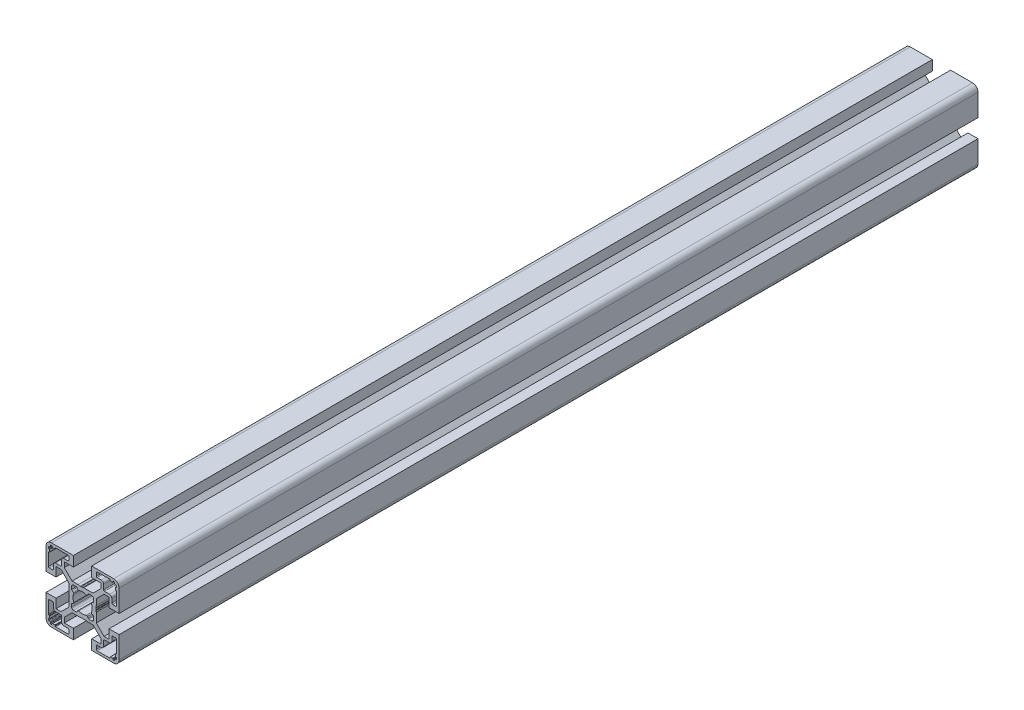
SolidWorks part; units mm, degrees
ref_plane "Front Plane" through (0, 0, 0) normal (0, 0, 1) x (1, 0, 0)
ref_plane "Top Plane" through (0, 0, 0) normal (0, 1, 0) x (1, 0, 0)
ref_plane "Right Plane" through (0, 0, 0) normal (1, 0, 0) x (0, 0, -1)
sketch "Sketch1" plane through (0, 0, 0) normal (0, 0, 1) x (1, 0, 0)
  line L0 (-11.7678, -10) -> (-14.5, -10)
  line L1 (-14.5, -10) -> (-14.5, -5)
  line L2 (-14.5, -5) -> (-20, -5)
  line L3 (-20, -5) -> (-20, -17)
  line L4 (-17, -20) -> (-5, -20)
  line L5 (-5, -20) -> (-5, -14.5)
  line L6 (-5, -14.5) -> (-10, -14.5)
  line L7 (-10, -14.5) -> (-10, -11.7678)
  line L8 (-10, -11.7678) -> (-5.7322, -7.5)
  line L9 (-5.7322, -7.5) -> (-0.6536, -7.5)
  line L10 (-0.4036, -7.433) -> (0, -7.2)
  line L11 (0, -7.2) -> (0.4036, -7.433)
  line L12 (0.9036, -7.433) -> (1.2189, -7.251)
  line L13 (1.2189, -7.251) -> (2.5, -7.5)
  line L14 (2.5, -7.5) -> (5.7322, -7.5)
  line L15 (5.7322, -7.5) -> (10, -11.7678)
  line L16 (10, -11.7678) -> (10, -14.5)
  line L17 (10, -14.5) -> (5, -14.5)
  line L18 (5, -14.5) -> (5, -20)
  line L19 (5, -20) -> (17, -20)
  line L20 (20, -17) -> (20, -5)
  line L21 (20, -5) -> (14.5, -5)
  line L22 (14.5, -5) -> (14.5, -10)
  line L23 (14.5, -10) -> (11.7678, -10)
  line L24 (11.7678, -10) -> (7.5, -5.7322)
  line L25 (7.5, -5.7322) -> (7.5, -0.6536)
  line L26 (7.433, -0.4036) -> (7.2, 0)
  line L27 (7.2, 0) -> (7.433, 0.4036)
  line L28 (7.433, 0.9036) -> (7.251, 1.2189)
  line L29 (7.251, 1.2189) -> (7.5, 2.5)
  line L30 (7.5, 2.5) -> (7.5, 5.7322)
  line L31 (7.5, 5.7322) -> (11.7678, 10)
  line L32 (11.7678, 10) -> (14.5, 10)
  line L33 (14.5, 10) -> (14.5, 5)
  line L34 (14.5, 5) -> (20, 5)
  line L35 (20, 5) -> (20, 17)
  line L36 (17, 20) -> (5, 20)
  line L37 (5, 20) -> (5, 14.5)
  line L38 (5, 14.5) -> (10, 14.5)
  line L39 (10, 14.5) -> (10, 11.7678)
  line L40 (10, 11.7678) -> (5.7322, 7.5)
  line L41 (5.7322, 7.5) -> (0.6536, 7.5)
  line L42 (0.4036, 7.433) -> (0, 7.2)
  line L43 (0, 7.2) -> (-0.4036, 7.433)
  line L44 (-0.9036, 7.433) -> (-1.2189, 7.251)
  line L45 (-1.2189, 7.251) -> (-2.5, 7.5)
  line L46 (-2.5, 7.5) -> (-5.7322, 7.5)
  line L47 (-5.7322, 7.5) -> (-10, 11.7678)
  line L48 (-10, 11.7678) -> (-10, 14.5)
  line L49 (-10, 14.5) -> (-5, 14.5)
  line L50 (-5, 14.5) -> (-5, 20)
  line L51 (-5, 20) -> (-17, 20)
  line L52 (-20, 17) -> (-20, 5)
  line L53 (-20, 5) -> (-14.5, 5)
  line L54 (-14.5, 5) -> (-14.5, 10)
  line L55 (-14.5, 10) -> (-11.7678, 10)
  line L56 (-11.7678, 10) -> (-7.5, 5.7322)
  line L57 (-7.5, 5.7322) -> (-7.5, 0.6536)
  line L58 (-7.433, 0.4036) -> (-7.2, 0)
  line L59 (-7.2, 0) -> (-7.433, -0.4036)
  line L60 (-7.433, -0.9036) -> (-7.251, -1.2189)
  line L61 (-7.251, -1.2189) -> (-7.5, -2.5)
  line L62 (-7.5, -2.5) -> (-7.5, -5.7322)
  line L63 (-7.5, -5.7322) -> (-11.7678, -10)
  line L64 (7.5, 16.5) -> (7.5, 18.2)
  line L65 (8, 18.7) -> (14.8, 18.7)
  line L66 (15, 18.5) -> (15, 18.2)
  line L67 (15.2, 18) -> (16.4, 18)
  line L68 (16.6, 18.2) -> (16.6, 18.5)
  line L69 (16.8, 18.7) -> (17.3, 18.7)
  line L70 (17.6, 18.4) -> (17.6, 17.9)
  line L71 (17.9, 17.6) -> (18.4, 17.6)
  line L72 (18.7, 17.3) -> (18.7, 16.8)
  line L73 (18.5, 16.6) -> (18.2, 16.6)
  line L74 (18, 16.4) -> (18, 15.2)
  line L75 (18.2, 15) -> (18.5, 15)
  line L76 (18.7, 14.8) -> (18.7, 8)
  line L77 (18.2, 7.5) -> (16.5, 7.5)
  line L78 (16, 8) -> (16, 10.2)
  line L79 (14.7, 11.5) -> (12, 11.5)
  line L80 (11.5, 12) -> (11.5, 14.7)
  line L81 (10.2, 16) -> (8, 16)
  line L82 (14.8, -18.7) -> (8, -18.7)
  line L83 (7.5, -18.2) -> (7.5, -16.5)
  line L84 (8, -16) -> (10.2, -16)
  line L85 (11.5, -14.7) -> (11.5, -12)
  line L86 (12, -11.5) -> (14.7, -11.5)
  line L87 (16, -10.2) -> (16, -8)
  line L88 (16.5, -7.5) -> (18.2, -7.5)
  line L89 (18.7, -8) -> (18.7, -14.8)
  line L90 (18.5, -15) -> (18.2, -15)
  line L91 (18, -15.2) -> (18, -16.4)
  line L92 (18.2, -16.6) -> (18.5, -16.6)
  line L93 (18.7, -16.8) -> (18.7, -17.3)
  line L94 (18.4, -17.6) -> (17.9, -17.6)
  line L95 (17.6, -17.9) -> (17.6, -18.4)
  line L96 (17.3, -18.7) -> (16.8, -18.7)
  line L97 (16.6, -18.5) -> (16.6, -18.2)
  line L98 (16.4, -18) -> (15.2, -18)
  line L99 (15, -18.2) -> (15, -18.5)
  line L100 (-18.7, 16.8) -> (-18.7, 17.3)
  line L101 (-18.4, 17.6) -> (-17.9, 17.6)
  line L102 (-17.6, 17.9) -> (-17.6, 18.4)
  line L103 (-17.3, 18.7) -> (-16.8, 18.7)
  line L104 (-16.6, 18.5) -> (-16.6, 18.2)
  line L105 (-16.4, 18) -> (-15.2, 18)
  line L106 (-15, 18.2) -> (-15, 18.5)
  line L107 (-14.8, 18.7) -> (-8, 18.7)
  line L108 (-7.5, 18.2) -> (-7.5, 16.5)
  line L109 (-8, 16) -> (-10.2, 16)
  line L110 (-11.5, 14.7) -> (-11.5, 12)
  line L111 (-12, 11.5) -> (-14.7, 11.5)
  line L112 (-16, 10.2) -> (-16, 8)
  line L113 (-16.5, 7.5) -> (-18.2, 7.5)
  line L114 (-18.7, 8) -> (-18.7, 14.8)
  line L115 (-18.5, 15) -> (-18.2, 15)
  line L116 (-18, 15.2) -> (-18, 16.4)
  line L117 (-18.2, 16.6) -> (-18.5, 16.6)
  line L118 (-18.7, -14.8) -> (-18.7, -8)
  line L119 (-18.2, -7.5) -> (-16.5, -7.5)
  line L120 (-16, -8) -> (-16, -10.2)
  line L121 (-14.7, -11.5) -> (-12, -11.5)
  line L122 (-11.5, -12) -> (-11.5, -14.7)
  line L123 (-10.2, -16) -> (-8, -16)
  line L124 (-7.5, -16.5) -> (-7.5, -18.2)
  line L125 (-8, -18.7) -> (-14.8, -18.7)
  line L126 (-15, -18.5) -> (-15, -18.2)
  line L127 (-15.2, -18) -> (-16.4, -18)
  line L128 (-16.6, -18.2) -> (-16.6, -18.5)
  line L129 (-16.8, -18.7) -> (-17.3, -18.7)
  line L130 (-17.6, -18.4) -> (-17.6, -17.9)
  line L131 (-17.9, -17.6) -> (-18.4, -17.6)
  line L132 (-18.7, -17.3) -> (-18.7, -16.8)
  line L133 (-18.5, -16.6) -> (-18.2, -16.6)
  line L134 (-18, -16.4) -> (-18, -15.2)
  line L135 (-18.2, -15) -> (-18.5, -15)
  line L136 (-6, 3.4907) -> (-6, 5)
  line L137 (-5, 6) -> (-3.4907, 6)
  line L138 (-3.0492, 5.7347) -> (-2.6892, 5.0577)
  line L139 (2.6892, 5.0577) -> (3.0492, 5.7347)
  line L140 (3.4907, 6) -> (5, 6)
  line L141 (6, 5) -> (6, 3.4907)
  line L142 (5.7347, 3.0492) -> (5.0577, 2.6892)
  line L143 (5.0577, -2.6892) -> (5.7347, -3.0492)
  line L144 (6, -3.4907) -> (6, -5)
  line L145 (5, -6) -> (3.4907, -6)
  line L146 (3.0492, -5.7347) -> (2.6892, -5.0577)
  line L147 (-2.6892, -5.0577) -> (-3.0492, -5.7347)
  line L148 (-3.4907, -6) -> (-5, -6)
  line L149 (-6, -5) -> (-6, -3.4907)
  line L150 (-5.7347, -3.0492) -> (-5.0577, -2.6892)
  line L151 (-5.0577, 2.6892) -> (-5.7347, 3.0492)
  arc A0 (-20, -17) -> (-17, -20) centre (-17, -17) ccw
  arc A1 (-0.6536, -7.5) -> (-0.4036, -7.433) centre (-0.6536, -7) ccw
  arc A2 (0.4036, -7.433) -> (0.9036, -7.433) centre (0.6536, -7) ccw
  arc A3 (17, -20) -> (20, -17) centre (17, -17) ccw
  arc A4 (7.5, -0.6536) -> (7.433, -0.4036) centre (7, -0.6536) ccw
  arc A5 (7.433, 0.4036) -> (7.433, 0.9036) centre (7, 0.6536) ccw
  arc A6 (20, 17) -> (17, 20) centre (17, 17) ccw
  arc A7 (0.6536, 7.5) -> (0.4036, 7.433) centre (0.6536, 7) ccw
  arc A8 (-0.4036, 7.433) -> (-0.9036, 7.433) centre (-0.6536, 7) ccw
  arc A9 (-17, 20) -> (-20, 17) centre (-17, 17) ccw
  arc A10 (-7.5, 0.6536) -> (-7.433, 0.4036) centre (-7, 0.6536) ccw
  arc A11 (-7.433, -0.4036) -> (-7.433, -0.9036) centre (-7, -0.6536) ccw
  arc A12 (8, 16) -> (7.5, 16.5) centre (8, 16.5) cw
  arc A13 (7.5, 18.2) -> (8, 18.7) centre (8, 18.2) cw
  arc A14 (14.8, 18.7) -> (15, 18.5) centre (14.8, 18.5) cw
  arc A15 (15, 18.2) -> (15.2, 18) centre (15.2, 18.2) ccw
  arc A16 (16.4, 18) -> (16.6, 18.2) centre (16.4, 18.2) ccw
  arc A17 (16.6, 18.5) -> (16.8, 18.7) centre (16.8, 18.5) cw
  arc A18 (17.3, 18.7) -> (17.6, 18.4) centre (17.3, 18.4) cw
  arc A19 (17.6, 17.9) -> (17.9, 17.6) centre (17.9, 17.9) ccw
  arc A20 (18.4, 17.6) -> (18.7, 17.3) centre (18.4, 17.3) cw
  arc A21 (18.7, 16.8) -> (18.5, 16.6) centre (18.5, 16.8) cw
  arc A22 (18.2, 16.6) -> (18, 16.4) centre (18.2, 16.4) ccw
  arc A23 (18, 15.2) -> (18.2, 15) centre (18.2, 15.2) ccw
  arc A24 (18.5, 15) -> (18.7, 14.8) centre (18.5, 14.8) cw
  arc A25 (18.7, 8) -> (18.2, 7.5) centre (18.2, 8) cw
  arc A26 (16.5, 7.5) -> (16, 8) centre (16.5, 8) cw
  arc A27 (16, 10.2) -> (14.7, 11.5) centre (14.7, 10.2) ccw
  arc A28 (12, 11.5) -> (11.5, 12) centre (12, 12) cw
  arc A29 (11.5, 14.7) -> (10.2, 16) centre (10.2, 14.7) ccw
  arc A30 (8, -18.7) -> (7.5, -18.2) centre (8, -18.2) cw
  arc A31 (7.5, -16.5) -> (8, -16) centre (8, -16.5) cw
  arc A32 (10.2, -16) -> (11.5, -14.7) centre (10.2, -14.7) ccw
  arc A33 (11.5, -12) -> (12, -11.5) centre (12, -12) cw
  arc A34 (14.7, -11.5) -> (16, -10.2) centre (14.7, -10.2) ccw
  arc A35 (16, -8) -> (16.5, -7.5) centre (16.5, -8) cw
  arc A36 (18.2, -7.5) -> (18.7, -8) centre (18.2, -8) cw
  arc A37 (18.7, -14.8) -> (18.5, -15) centre (18.5, -14.8) cw
  arc A38 (18.2, -15) -> (18, -15.2) centre (18.2, -15.2) ccw
  arc A39 (18, -16.4) -> (18.2, -16.6) centre (18.2, -16.4) ccw
  arc A40 (18.5, -16.6) -> (18.7, -16.8) centre (18.5, -16.8) cw
  arc A41 (18.7, -17.3) -> (18.4, -17.6) centre (18.4, -17.3) cw
  arc A42 (17.9, -17.6) -> (17.6, -17.9) centre (17.9, -17.9) ccw
  arc A43 (17.6, -18.4) -> (17.3, -18.7) centre (17.3, -18.4) cw
  arc A44 (16.8, -18.7) -> (16.6, -18.5) centre (16.8, -18.5) cw
  arc A45 (16.6, -18.2) -> (16.4, -18) centre (16.4, -18.2) ccw
  arc A46 (15.2, -18) -> (15, -18.2) centre (15.2, -18.2) ccw
  arc A47 (15, -18.5) -> (14.8, -18.7) centre (14.8, -18.5) cw
  arc A48 (-18.5, 16.6) -> (-18.7, 16.8) centre (-18.5, 16.8) cw
  arc A49 (-18.7, 17.3) -> (-18.4, 17.6) centre (-18.4, 17.3) cw
  arc A50 (-17.9, 17.6) -> (-17.6, 17.9) centre (-17.9, 17.9) ccw
  arc A51 (-17.6, 18.4) -> (-17.3, 18.7) centre (-17.3, 18.4) cw
  arc A52 (-16.8, 18.7) -> (-16.6, 18.5) centre (-16.8, 18.5) cw
  arc A53 (-16.6, 18.2) -> (-16.4, 18) centre (-16.4, 18.2) ccw
  arc A54 (-15.2, 18) -> (-15, 18.2) centre (-15.2, 18.2) ccw
  arc A55 (-15, 18.5) -> (-14.8, 18.7) centre (-14.8, 18.5) cw
  arc A56 (-8, 18.7) -> (-7.5, 18.2) centre (-8, 18.2) cw
  arc A57 (-7.5, 16.5) -> (-8, 16) centre (-8, 16.5) cw
  arc A58 (-10.2, 16) -> (-11.5, 14.7) centre (-10.2, 14.7) ccw
  arc A59 (-11.5, 12) -> (-12, 11.5) centre (-12, 12) cw
  arc A60 (-14.7, 11.5) -> (-16, 10.2) centre (-14.7, 10.2) ccw
  arc A61 (-16, 8) -> (-16.5, 7.5) centre (-16.5, 8) cw
  arc A62 (-18.2, 7.5) -> (-18.7, 8) centre (-18.2, 8) cw
  arc A63 (-18.7, 14.8) -> (-18.5, 15) centre (-18.5, 14.8) cw
  arc A64 (-18.2, 15) -> (-18, 15.2) centre (-18.2, 15.2) ccw
  arc A65 (-18, 16.4) -> (-18.2, 16.6) centre (-18.2, 16.4) ccw
  arc A66 (-18.5, -15) -> (-18.7, -14.8) centre (-18.5, -14.8) cw
  arc A67 (-18.7, -8) -> (-18.2, -7.5) centre (-18.2, -8) cw
  arc A68 (-16.5, -7.5) -> (-16, -8) centre (-16.5, -8) cw
  arc A69 (-16, -10.2) -> (-14.7, -11.5) centre (-14.7, -10.2) ccw
  arc A70 (-12, -11.5) -> (-11.5, -12) centre (-12, -12) cw
  arc A71 (-11.5, -14.7) -> (-10.2, -16) centre (-10.2, -14.7) ccw
  arc A72 (-8, -16) -> (-7.5, -16.5) centre (-8, -16.5) cw
  arc A73 (-7.5, -18.2) -> (-8, -18.7) centre (-8, -18.2) cw
  arc A74 (-14.8, -18.7) -> (-15, -18.5) centre (-14.8, -18.5) cw
  arc A75 (-15, -18.2) -> (-15.2, -18) centre (-15.2, -18.2) ccw
  arc A76 (-16.4, -18) -> (-16.6, -18.2) centre (-16.4, -18.2) ccw
  arc A77 (-16.6, -18.5) -> (-16.8, -18.7) centre (-16.8, -18.5) cw
  arc A78 (-17.3, -18.7) -> (-17.6, -18.4) centre (-17.3, -18.4) cw
  arc A79 (-17.6, -17.9) -> (-17.9, -17.6) centre (-17.9, -17.9) ccw
  arc A80 (-18.4, -17.6) -> (-18.7, -17.3) centre (-18.4, -17.3) cw
  arc A81 (-18.7, -16.8) -> (-18.5, -16.6) centre (-18.5, -16.8) cw
  arc A82 (-18.2, -16.6) -> (-18, -16.4) centre (-18.2, -16.4) ccw
  arc A83 (-18, -15.2) -> (-18.2, -15) centre (-18.2, -15.2) ccw
  arc A84 (-5.7347, 3.0492) -> (-6, 3.4907) centre (-5.5, 3.4907) cw
  arc A85 (-6, 5) -> (-5, 6) centre (-5, 5) cw
  arc A86 (-3.4907, 6) -> (-3.0492, 5.7347) centre (-3.4907, 5.5) cw
  arc A87 (-2.6892, 5.0577) -> (-2.0523, 4.8322) centre (-2.2478, 5.2925) ccw
  arc A88 (-2.0523, 4.8322) -> (2.0523, 4.8322) centre (0, 0) cw
  arc A89 (2.0523, 4.8322) -> (2.6892, 5.0577) centre (2.2478, 5.2925) ccw
  arc A90 (3.0492, 5.7347) -> (3.4907, 6) centre (3.4907, 5.5) cw
  arc A91 (5, 6) -> (6, 5) centre (5, 5) cw
  arc A92 (6, 3.4907) -> (5.7347, 3.0492) centre (5.5, 3.4907) cw
  arc A93 (5.0577, 2.6892) -> (4.8322, 2.0523) centre (5.2925, 2.2478) ccw
  arc A94 (4.8322, 2.0523) -> (4.8322, -2.0523) centre (0, 0) cw
  arc A95 (4.8322, -2.0523) -> (5.0577, -2.6892) centre (5.2925, -2.2478) ccw
  arc A96 (5.7347, -3.0492) -> (6, -3.4907) centre (5.5, -3.4907) cw
  arc A97 (6, -5) -> (5, -6) centre (5, -5) cw
  arc A98 (3.4907, -6) -> (3.0492, -5.7347) centre (3.4907, -5.5) cw
  arc A99 (2.6892, -5.0577) -> (2.0523, -4.8322) centre (2.2478, -5.2925) ccw
  arc A100 (2.0523, -4.8322) -> (-2.0523, -4.8322) centre (0, 0) cw
  arc A101 (-2.0523, -4.8322) -> (-2.6892, -5.0577) centre (-2.2478, -5.2925) ccw
  arc A102 (-3.0492, -5.7347) -> (-3.4907, -6) centre (-3.4907, -5.5) cw
  arc A103 (-5, -6) -> (-6, -5) centre (-5, -5) cw
  arc A104 (-6, -3.4907) -> (-5.7347, -3.0492) centre (-5.5, -3.4907) cw
  arc A105 (-5.0577, -2.6892) -> (-4.8322, -2.0523) centre (-5.2925, -2.2478) ccw
  arc A106 (-4.8322, -2.0523) -> (-4.8322, 2.0523) centre (0, 0) cw
  arc A107 (-4.8322, 2.0523) -> (-5.0577, 2.6892) centre (-5.2925, 2.2478) ccw
extrude "Boss-Extrude1" add sketch "Sketch1" against normal blind 470
